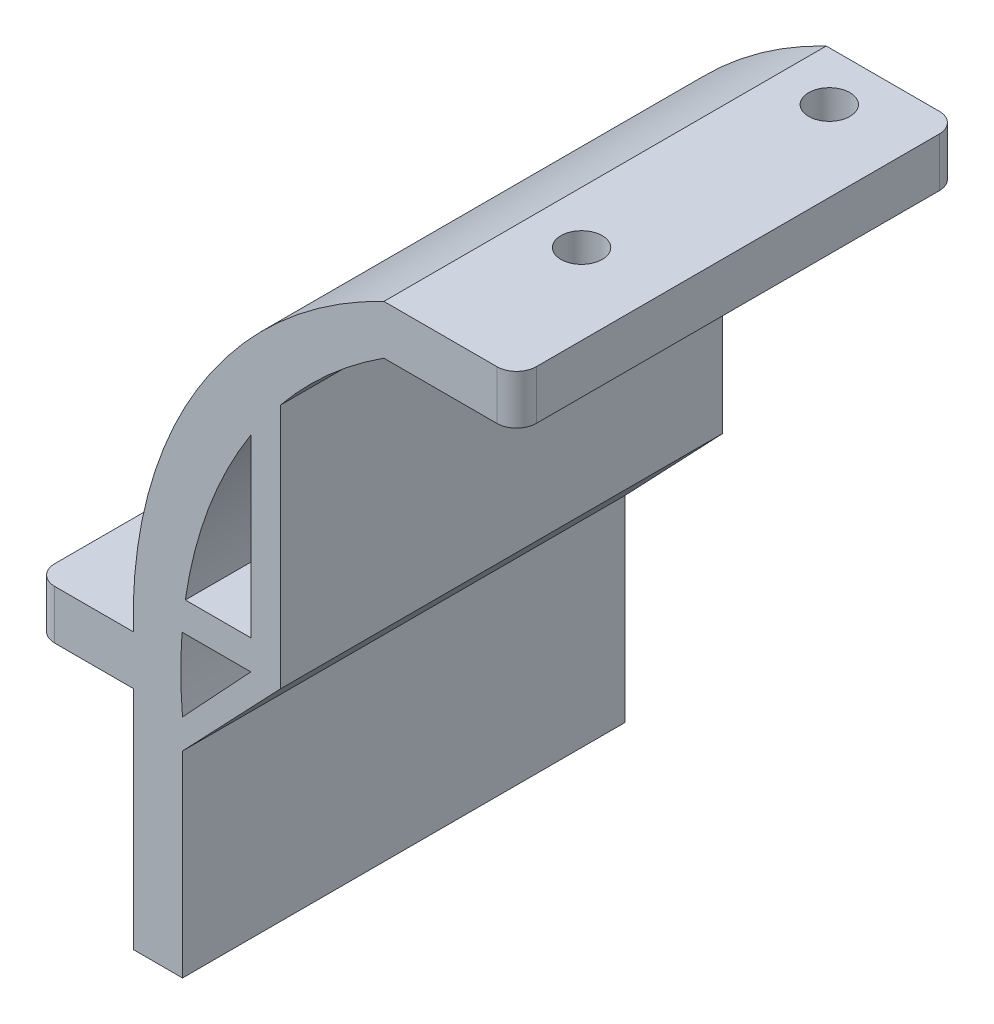
SolidWorks part; units mm, degrees
ref_plane "Front Plane" through (0, 0, 0) normal (0, 0, 1) x (1, 0, 0)
ref_plane "Top Plane" through (0, 0, 0) normal (0, 1, 0) x (1, 0, 0)
ref_plane "Right Plane" through (0, 0, 0) normal (1, 0, 0) x (0, 0, -1)
sketch "Sketch3" plane through (0, 0, 0) normal (0, 0, 1) x (1, 0, 0)
  line L5 (8.4348, 262.2647) -> (-5.0652, 262.2647)
  line L6 (8.4348, 262.2647) -> (8.4348, 257.2647)
  line L7 (8.4348, 257.2647) -> (-5.0652, 257.2647)
  line L8 (-5.0652, 262.2647) -> (-5.0652, 257.2647)
  line L9 (-40.5516, 215.4144) -> (-30.5516, 215.4144)
  line L10 (-40.5516, 215.4144) -> (-40.5516, 220.4144)
  line L11 (-40.5516, 220.4144) -> (-30.5516, 220.4144)
  line L12 (-30.5516, 215.4144) -> (-30.5516, 220.4144)
  line L13 (-30.5516, 215.4144) -> (-25.5516, 215.4144)
  line L14 (-30.5516, 215.4144) -> (-30.5516, 192.4144)
  line L15 (-30.5516, 192.4144) -> (-25.5516, 192.4144)
  line L16 (-25.5516, 215.4144) -> (-25.5516, 192.4144)
  arc A0 (-30.5516, 220.4144) -> (-5.0652, 262.2647) centre (14.4298, 221.7068) cw
  arc A1 (-5.0652, 257.2647) -> (-25.5516, 215.4144) centre (19.2704, 219.4126) ccw
  dimension "D8" = 45
  dimension "D9" = 45
  dimension "D3" = 13.5
  dimension "D4" = 5
  dimension "D6" = 10
  dimension "D7" = 5
extrude "Boss-Extrude1" add sketch "Sketch3" along normal blind 45 contours A1 L8 A0 L12 L13 | L5 L8 L7 L6 | L9 L12 L11 L10 | L16 L13 L14 L15
fillet "Fillet1" radius 2 4 edges at (-40.5516, 217.9144, 0) (-40.5516, 217.9144, 45) (8.4348, 259.7647, 0) (8.4348, 259.7647, 45)
sketch "Sketch5" plane through (0, 262.2647, 0) normal (0, 1, 0) x (1, 0, 0)
  line L0 (-5.0652, -45) -> (-5.0652, 0) construction
  line L2 (6.4348, -45) -> (-5.0652, -45) construction
  circle A0 centre (0.2448, -40) radius 2.1
  circle A2 centre (0.2448, -14.8) radius 2.1
  dimension "D1" = 5.31
  dimension "D2" = 4.2
  dimension "D4" = 5
  dimension "D6" = 4.2
extrude "Cut-Extrude2" cut sketch "Sketch5" against normal blind 45
sketch "Sketch6" plane through (0, 220.4144, 0) normal (0, 1, 0) x (1, 0, 0)
  line L0 (-38.5516, -45) -> (-30.5516, -45) construction
  line L1 (-40.5516, -43) -> (-40.5516, -2) construction
  line L2 (-38.5516, 0) -> (-30.5516, 0) construction
  circle A0 centre (-35.5516, -10) radius 2.1
  circle A1 centre (-35.5516, -35) radius 2.1
  dimension "D1" = 4.2
  dimension "D2" = 4.2
  dimension "D3" = 10
  dimension "D4" = 5
  dimension "D5" = 5
  dimension "D6" = 10
extrude "Cut-Extrude3" cut sketch "Sketch6" against normal blind 45
sketch "Sketch7" plane through (0, 262.2647, 0) normal (0, 1, 0) x (1, 0, 0)
  line L1 (-3.0108, -10.6298) -> (5.1997, -10.6298)
  line L2 (-3.0108, -10.6298) -> (-3.0108, -43.2171)
  line L3 (-3.0108, -43.2171) -> (5.1997, -43.2171)
  line L4 (5.1997, -10.6298) -> (5.1997, -43.2171)
extrude "Boss-Extrude2" add sketch "Sketch7" against normal up to surface (5 mm away) contours L2 L1 L4 L3 up to face at (0.2448, 257.2647, 37.9)
sketch "Sketch8" plane through (0, 262.2647, 0) normal (0, 1, 0) x (1, 0, 0)
  line L0 (-5.0652, -35.2) -> (8.4348, -35.2)
  line L1 (-5.0652, -45) -> (-5.0652, 0) construction
  line L2 (8.4348, -43) -> (8.4348, -2) construction
  line L3 (6.4348, 0) -> (-5.0652, 0) construction
  circle A0 centre (0.2448, -5) radius 2.1
  circle A1 centre (0.2448, -30.2) radius 2.1
  dimension "D1" = 4.2
  dimension "D2" = 4.2
  dimension "D3" = 5
  dimension "D4" = 5
  dimension "D6" = 5.31
  dimension "D7" = 5.31
  dimension "D5" = 35.2
extrude "Cut-Extrude5" cut sketch "Sketch8" against normal blind 45 contours A0 | A1
sketch "Sketch9" plane through (0, 0, 45) normal (0, 0, 1) x (1, 0, 0)
  line L0 (-25.5974, 222.8598) -> (-15.5974, 222.8598)
  line L1 (-15.5974, 222.8598) -> (-15.5974, 247.8598)
  line L2 (-18.5974, 243.7238) -> (-18.5974, 225.8598)
  line L3 (-18.5974, 225.8598) -> (-25.2654, 225.8598)
  line L4 (-15.5974, 222.8598) -> (-25.5516, 212.4144)
  line L5 (-25.5516, 215.4144) -> (-25.5516, 192.4144) construction
  line L6 (-18.5974, 222.8598) -> (-25.5516, 215.4144)
  arc A0 (-5.0652, 257.2647) -> (-25.5516, 215.4144) centre (19.2704, 219.4126) ccw construction
  point P8 (-20.5974, 222.8598)
  line M11 (-25.5516, 192.4144) -> (-25.5516, 215.4144)
  arc M12 (-25.5516, 215.4144) -> (-5.0652, 257.2647) centre (19.2704, 219.4126) cw
  dimension "D1" = 25
  dimension "D2" = 10
  dimension "D3" = 3
  dimension "D4" = 3
  dimension "D5" = 3
extrude "Boss-Extrude3" add sketch "Sketch9" against normal through all contours L2 L3 L0 L1 M12 | L0 L6 L4 M11
